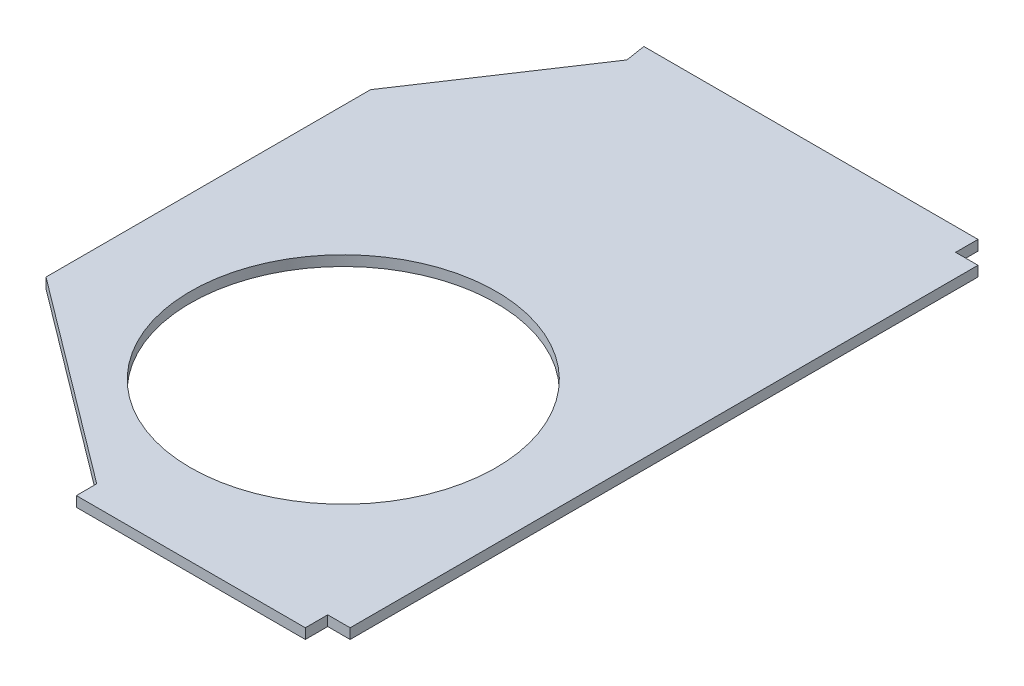
SolidWorks part; units mm, degrees
ref_plane "Front Plane" through (0, 0, 0) normal (0, 0, 1) x (1, 0, 0)
ref_plane "Top Plane" through (0, 0, 0) normal (0, 1, 0) x (1, 0, 0)
ref_plane "Right Plane" through (0, 0, 0) normal (1, 0, 0) x (0, 0, -1)
sketch "Sketch1" plane through (0, 0, 0) normal (0, 1, 0) x (1, 0, 0)
  line L1 (0, 0) -> (246.7776, 0)
  line L3 (-103.2224, 660.3612) -> (246.7776, 660.3612)
  line L4 (246.7776, 0) -> (246.7776, 660.3612)
  line L14 (-200.678, 330.1806) -> (-200.678, 489.4756)
  line L18 (-200.678, 330.1806) -> (-200.678, 170.8856)
  line L20 (-103.2224, 660.3612) -> (-100.1336, 640.6012)
  line L21 (-100.1336, 640.6012) -> (-200.678, 489.4756)
  line L22 (0, 0) -> (0, 20)
  line L23 (0, 20) -> (-200.678, 170.8856)
  point P5 (-101.678, 650.4812)
  point P7 (246.7776, 330.1806)
  dimension "D1" = 350
  dimension "D2" = 668.38
  dimension "D3" = 159.295
  dimension "D4" = 159.295
  dimension "D5" = 20
  dimension "D6" = 20
  dimension "D7" = 99
extrude "Boss-Extrude2" add sketch "Sketch1" along normal blind 10
sketch "Sketch4" plane through (0, 10, 0) normal (0, 1, 0) x (1, 0, 0)
  line L2 (0, 358.38) -> (-20, 358.38)
  line L3 (0, 358.38) -> (0, 338.38)
  line L4 (0, 338.38) -> (-20, 338.38)
  line L5 (-20, 358.38) -> (-20, 338.38)
  dimension "D2" = 20
  dimension "D3" = 20
extrude "Cut-Extrude1" cut sketch "Sketch4" against normal blind 10
sketch "Sketch5" plane through (0, 0, 0) normal (0, -1, 0) x (1, 0, 0)
  line L1 (246.7776, -660.3612) -> (224.7776, -660.3612)
  line L2 (246.7776, -660.3612) -> (246.7776, -638.3612)
  line L3 (246.7776, -638.3612) -> (224.7776, -638.3612)
  line L4 (224.7776, -660.3612) -> (224.7776, -638.3612)
  line L5 (246.7776, 0) -> (224.7776, 0)
  line L6 (246.7776, 0) -> (246.7776, -22)
  line L7 (246.7776, -22) -> (224.7776, -22)
  line L8 (224.7776, 0) -> (224.7776, -22)
  dimension "D1" = 22
  dimension "D2" = 22
  dimension "D3" = 22
  dimension "D4" = 22
extrude "Cut-Extrude2" cut sketch "Sketch5" against normal through all
sketch "Sketch6" plane through (0, 10, 0) normal (0, 1, 0) x (1, 0, 0)
  circle A0 centre (32.341, 229.6841) radius 150 construction
  circle A1 centre (32.341, 229.6841) radius 150
extrude "Cut-Extrude3" cut sketch "Sketch6" against normal through all
